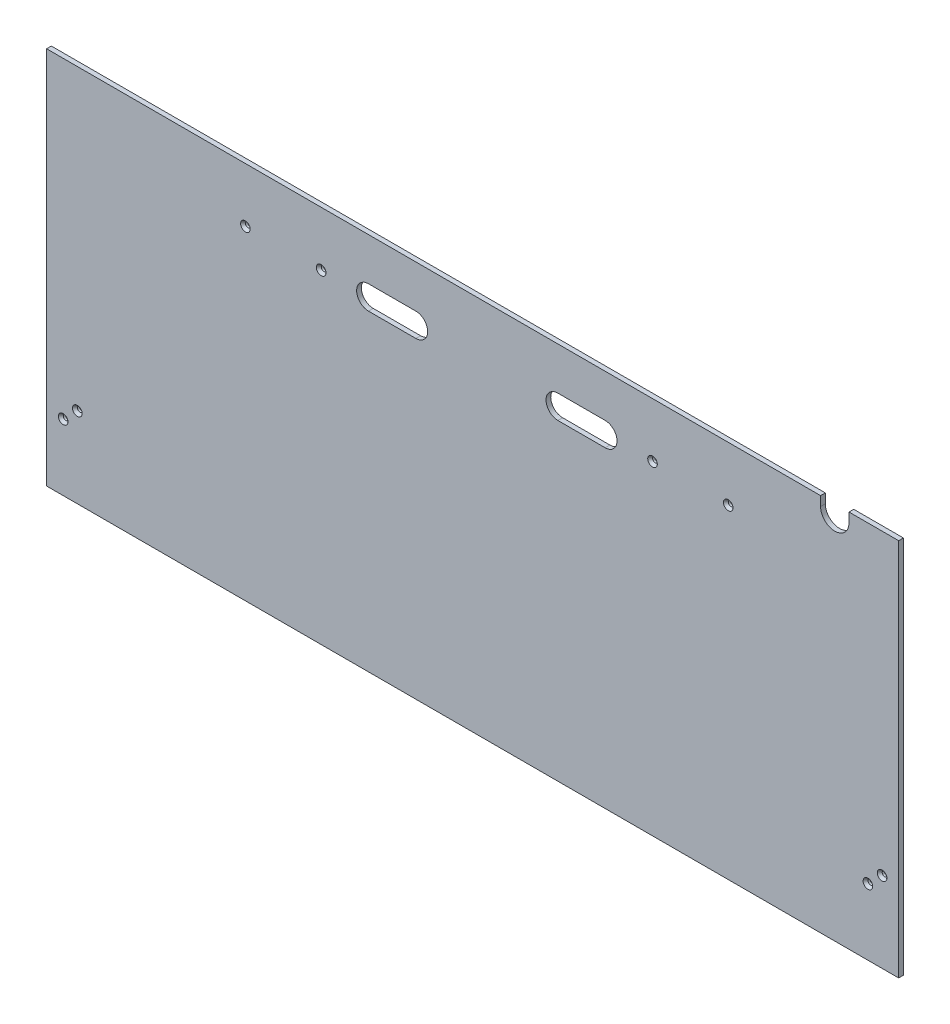
SolidWorks part; units mm, degrees
material "PC High Viscosity"
ref_plane "Front Plane" through (0, 0, 0) normal (0, 0, 1) x (1, 0, 0)
ref_plane "Top Plane" through (0, 0, 0) normal (0, 1, 0) x (1, 0, 0)
ref_plane "Right Plane" through (0, 0, 0) normal (1, 0, 0) x (0, 0, -1)
sketch "Sketch1" plane through (0, 0, 0) normal (0, 0, 1) x (1, 0, 0)
  line L1 (0, 0) -> (1143, 0)
  line L2 (0, 0) -> (0, 508)
  line L3 (0, 508) -> (1143, 508)
  line L4 (1143, 0) -> (1143, 508)
  dimension "D1" = 508
  dimension "D2" = 1143
extrude "Boss-Extrude1" add sketch "Sketch1" along normal blind 6.35
sketch "Sketch2" plane through (0, 0, 6.35) normal (0, 0, 1) x (1, 0, 0)
  line L0 (431.8, 434.975) -> (495.3, 434.975) construction
  line L1 (431.8, 450.85) -> (495.3, 450.85)
  line L2 (431.8, 419.1) -> (495.3, 419.1)
  line L3 (685.8, 434.975) -> (749.3, 434.975) construction
  line L4 (685.8, 450.85) -> (749.3, 450.85)
  line L5 (685.8, 419.1) -> (749.3, 419.1)
  line L6 (1143, 0) -> (1143, 508) construction
  line L7 (1143, 508) -> (0, 508) construction
  arc A0 (431.8, 450.85) -> (431.8, 419.1) centre (431.8, 434.975) ccw
  arc A1 (495.3, 419.1) -> (495.3, 450.85) centre (495.3, 434.975) ccw
  arc A2 (685.8, 450.85) -> (685.8, 419.1) centre (685.8, 434.975) ccw
  arc A3 (749.3, 419.1) -> (749.3, 450.85) centre (749.3, 434.975) ccw
  point P2 (463.55, 434.975)
  point P7 (717.55, 434.975)
  dimension "D5" = 15.875
  dimension "D1" = 393.7
  dimension "D2" = 457.2
  dimension "D3" = 647.7
  dimension "D4" = 711.2
  dimension "D6" = 73.025
extrude "Cut-Extrude1" cut sketch "Sketch2" against normal through all
hole_wizard "CSK for 1/4 Flat Head Machine Screw1" positions "Sketch3" profile "Sketch5" countersink size "1/4" standard "ANSI Inch" end condition up to next
sketch "Sketch3" plane through (0, 0, 6.35) normal (0, 0, 1) x (1, 0, 0)
  line L0 (1143, 508) -> (0, 508) construction
  line L1 (1143, 0) -> (1143, 508) construction
  line L2 (1143, 508) -> (0, 508) construction
  point P0 (914.4, 434.975)
  point P2 (812.8, 434.975)
  point P4 (368.3, 434.975)
  point P6 (266.7, 434.975)
  point P8 (1120.775, 107.95)
  point P10 (1101.725, 88.9)
  point P12 (41.275, 107.95)
  point P14 (22.225, 88.9)
  dimension "D1" = 73.025
  dimension "D2" = 228.6
  dimension "D3" = 330.2
  dimension "D4" = 774.7
  dimension "D5" = 876.3
  dimension "D6" = 400.05
  dimension "D7" = 419.1
  dimension "D8" = 22.225
  dimension "D9" = 41.275
  dimension "D10" = 1101.725
  dimension "D11" = 1120.775
sketch "Sketch5" plane through (914.4, 434.975, 6.35) normal (1, 0, 0) x (0, -1, 0)
  line L0 (0, 0) -> (0, 6.35)
  line L1 (0, 6.35) -> (3.3782, 6.35)
  line L2 (3.3782, 6.35) -> (3.3782, 3.5209)
  line L3 (3.3782, 3.5209) -> (6.4389, 0)
  line L5 (6.4389, 0) -> (0, 0)
  line L6 (-3.3782, 3.5209) -> (-6.4389, 0) construction
  line L11 (0, -6.35) -> (0, 107.95) construction
  dimension "Thru Hole Dia." = 6.7564
  dimension "Thru Hole Depth" = 6.35
  dimension "Near C'Sink Dia." = 12.8778
  dimension "Near C'Sink Angle" = 82
sketch "Sketch6" plane through (0, 0, 6.35) normal (0, 0, 1) x (1, 0, 0)
  line L0 (1143, 508) -> (0, 508) construction
  line L1 (1038.225, 508) -> (1076.325, 508)
  line L2 (1038.225, 508) -> (1038.225, 495.3)
  line L4 (1076.325, 508) -> (1076.325, 495.3)
  line L5 (1143, 0) -> (1143, 508) construction
  arc A0 (1076.325, 495.3) -> (1038.225, 495.3) centre (1057.275, 495.3) cw
  dimension "D3" = 104.775
  dimension "D1" = 12.7
  dimension "D2" = 66.675
extrude "Cut-Extrude2" cut sketch "Sketch6" against normal through all
